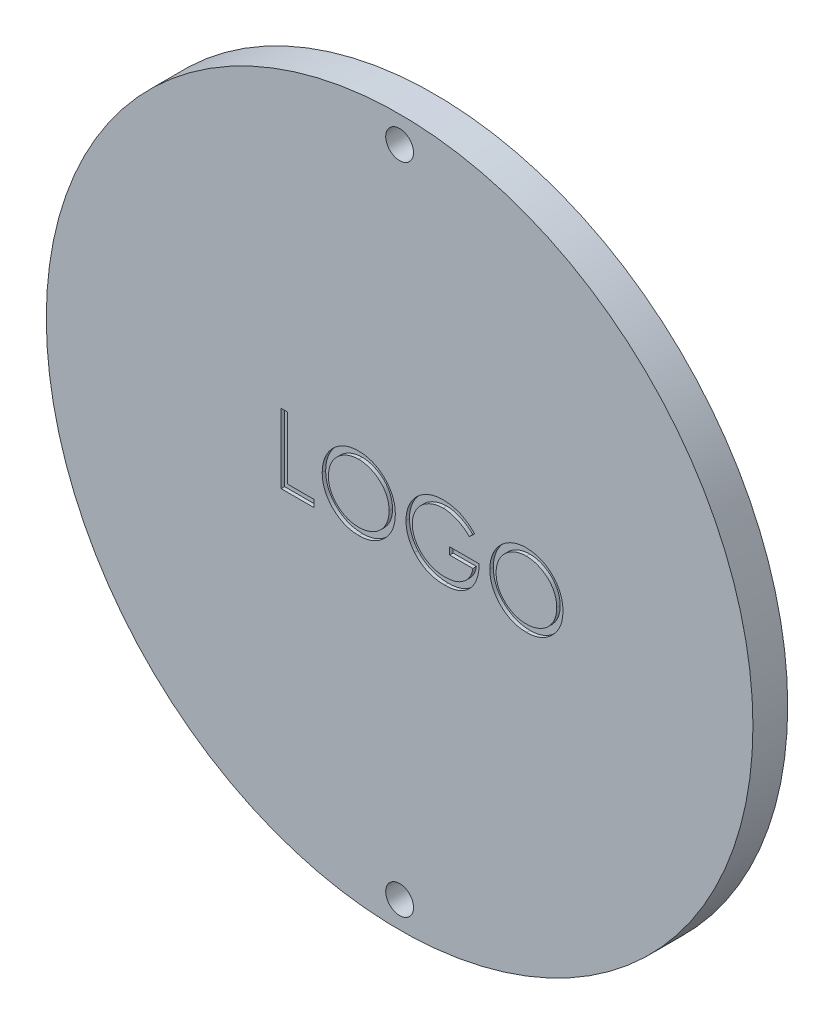
SolidWorks part; units mm, degrees
ref_plane "Plan de face" through (0, 0, 0) normal (0, 0, 1) x (1, 0, 0)
ref_plane "Plan de dessus" through (0, 0, 0) normal (0, 1, 0) x (1, 0, 0)
ref_plane "Plan de droite" through (0, 0, 0) normal (1, 0, 0) x (0, 0, -1)
sketch "Esquisse1" plane through (0, 0, 0) normal (0, 0, 1) x (1, 0, 0)
  circle A0 centre (0, 0) radius 50.8
  dimension "D1" = 101.6
extrude "Boss.-Extru.1" add sketch "Esquisse1" along normal blind 5
sketch "Esquisse2" plane through (0, 0, 5) normal (0, 0, 1) x (1, 0, 0)
  line L0 (0, -2.75) -> (0, 2.75) construction
  circle A0 centre (0, 47) radius 2
  circle A1 centre (0, -47) radius 2
  point P10 (0, 0)
  dimension "D1" = 4
  dimension "D2" = 47
  dimension "D3" = 2
extrude "Enlèv. mat.-Extru.1" cut sketch "Esquisse2" against normal through all
sketch "Esquisse4" plane through (0, 0, 5) normal (0, 0, 1) x (1, 0, 0)
  text T0 "LOGO" font "Century Gothic" height 10
extrude "Enlèv. mat.-Extru.2" cut sketch "Esquisse4" against normal blind 0.5
